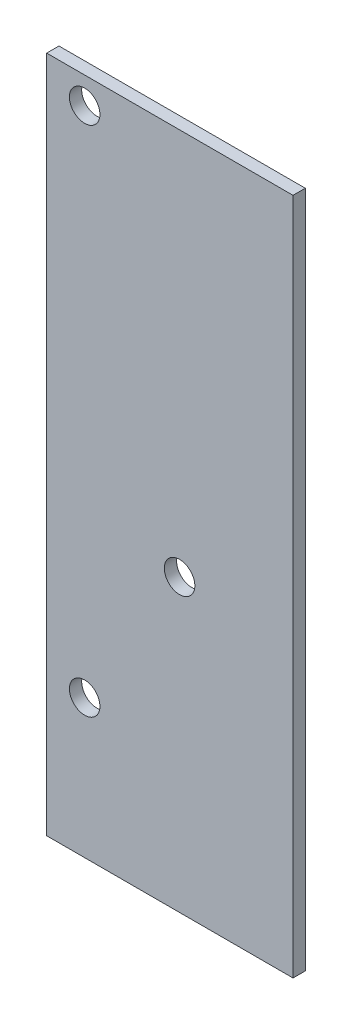
SolidWorks part; units mm, degrees
material "Al 6061-T6"
ref_plane "Front Plane" through (0, 0, 0) normal (0, 0, 1) x (1, 0, 0)
ref_plane "Top Plane" through (0, 0, 0) normal (0, 1, 0) x (1, 0, 0)
ref_plane "Right Plane" through (0, 0, 0) normal (1, 0, 0) x (0, 0, -1)
sketch "Sketch1" plane through (0, 0, 0) normal (0, 0, 1) x (1, 0, 0)
  line L1 (20.5994, -56.6801) -> (-20.5994, -56.6801)
  line L2 (20.5994, -56.6801) -> (20.5994, 56.6801)
  line L3 (20.5994, 56.6801) -> (-20.5994, 56.6801)
  line L4 (-20.5994, -56.6801) -> (-20.5994, 56.6801)
  line L5 (20.5994, -56.6801) -> (-20.5994, 56.6801) construction
  line L6 (20.5994, 56.6801) -> (-20.5994, -56.6801) construction
  point P0 (0, 0)
  dimension "D1" = 41.1988
  dimension "D2" = 113.3602
extrude "Boss-Extrude1" add sketch "Sketch1" along normal blind 2.0549
hole_wizard "#10 Clearance Hole1" positions "Sketch2" profile "Sketch3" hole size "#10" standard "ANSI Inch" end condition through all
sketch "Sketch2" plane through (0, 0, 2.0549) normal (0, 0, 1) x (1, 0, 0)
  line L0 (-20.5994, 56.6801) -> (-20.5994, -56.6801) construction
  line L1 (-20.5994, -56.6801) -> (20.5994, -56.6801) construction
  point P0 (-14.2494, 52.2351)
  point P2 (1.6256, -8.0899)
  point P4 (-14.2494, -33.4899)
  dimension "D1" = 6.35
  dimension "D2" = 6.35
  dimension "D3" = 22.225
  dimension "D4" = 23.1902
  dimension "D5" = 48.5902
  dimension "D6" = 108.9152
sketch "Sketch3" plane through (-14.2494, 52.2351, 2.0549) normal (1, 0, 0) x (0, -1, 0)
  line L0 (0, 0) -> (0, 2.0549)
  line L1 (0, 2.0549) -> (2.5527, 2.0549)
  line L2 (2.5527, 2.0549) -> (2.5527, 0)
  line L5 (2.5527, 0) -> (0, 0)
  line L11 (0, -6.35) -> (0, 107.95) construction
  dimension "Thru Hole Dia." = 5.1054
  dimension "Thru Hole Depth" = 2.0549
